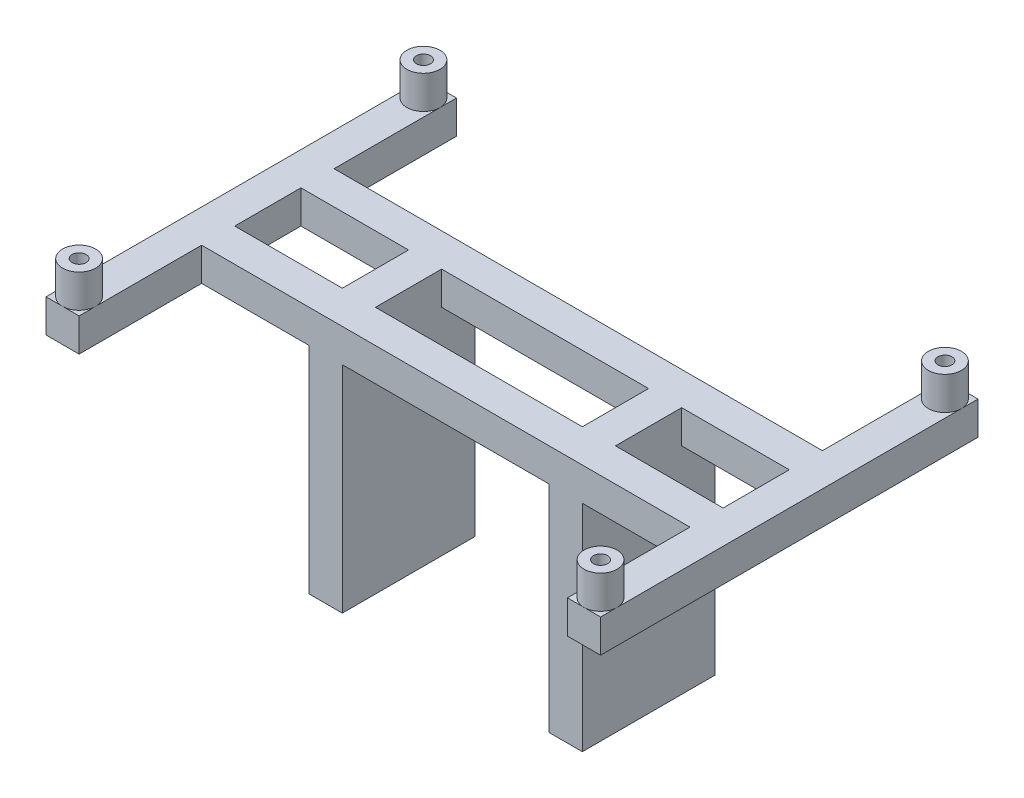
SolidWorks part; units mm, degrees
ref_plane "Front Plane" through (0, 0, 0) normal (0, 0, 1) x (1, 0, 0)
ref_plane "Top Plane" through (0, 0, 0) normal (0, 1, 0) x (1, 0, 0)
ref_plane "Right Plane" through (0, 0, 0) normal (1, 0, 0) x (0, 0, -1)
sketch "Sketch1" plane through (0, 0, 0) normal (0, 1, 0) x (1, 0, 0)
  line L28 (20.955, -5.08) -> (37.465, -5.08)
  line L31 (-42.545, 28.956) -> (-37.465, 28.956)
  line L32 (-42.545, 28.956) -> (-42.545, -28.956)
  line L33 (-42.545, -28.956) -> (-37.465, -28.956)
  line L34 (-37.465, 28.956) -> (-37.465, 10.16)
  line L35 (37.465, 28.956) -> (42.545, 28.956)
  line L36 (37.465, 28.956) -> (37.465, 10.16)
  line L37 (37.465, -28.956) -> (42.545, -28.956)
  line L38 (42.545, 28.956) -> (42.545, -28.956)
  line L39 (-37.465, 10.16) -> (37.465, 10.16)
  line L41 (-37.465, 5.08) -> (-20.955, 5.08)
  line L43 (-37.465, -5.08) -> (-20.955, -5.08)
  line L45 (-37.465, -10.16) -> (37.465, -10.16)
  line L48 (-20.955, 5.08) -> (-20.955, -5.08)
  line L50 (-15.875, 5.08) -> (-15.875, -5.08)
  line L52 (15.875, 5.08) -> (15.875, -5.08)
  line L54 (20.955, 5.08) -> (20.955, -5.08)
  line L55 (20.955, 5.08) -> (37.465, 5.08)
  line L56 (37.465, 5.08) -> (37.465, -5.08)
  line L57 (37.465, -10.16) -> (37.465, -28.956)
  line L58 (-15.875, -5.08) -> (15.875, -5.08)
  line L59 (-15.875, 5.08) -> (15.875, 5.08)
  line L60 (-37.465, 5.08) -> (-37.465, -5.08)
  line L61 (-37.465, -10.16) -> (-37.465, -28.956)
  point P25 (15.875, 0)
  point P26 (37.465, 0)
  point P27 (42.545, 0)
  point P28 (-20.955, 0)
  point P29 (0, 5.08)
  dimension "D1" = 57.912
  dimension "D2" = 5.08
  dimension "D3" = 5.08
  dimension "D4" = 20.32
  dimension "D5" = 41.91
  dimension "D6" = 5.08
  dimension "D7" = 5.08
  dimension "D8" = 5.08
  dimension "D9" = 85.09
extrude "Boss-Extrude1" add sketch "Sketch1" along normal blind 5.08
sketch "Sketch2" plane through (0, 0, 0) normal (0, -1, 0) x (1, 0, 0)
  line L1 (-20.955, 10.16) -> (-15.875, 10.16)
  line L2 (-20.955, 10.16) -> (-20.955, -10.16)
  line L3 (-20.955, -10.16) -> (-15.875, -10.16)
  line L4 (-15.875, 10.16) -> (-15.875, -10.16)
  line L6 (15.875, 10.16) -> (20.955, 10.16)
  line L7 (15.875, 10.16) -> (15.875, -10.16)
  line L8 (15.875, -10.16) -> (20.955, -10.16)
  line L9 (20.955, 10.16) -> (20.955, -10.16)
  line L12 (-20.955, 5.08) -> (-20.955, -5.08) construction
  line L13 (-15.875, -5.08) -> (-15.875, 5.08) construction
  line L14 (37.465, -10.16) -> (-37.465, -10.16) construction
  line L15 (-37.465, 10.16) -> (37.465, 10.16) construction
  line L16 (15.875, 5.08) -> (15.875, -5.08) construction
  line L17 (20.955, -5.08) -> (20.955, 5.08) construction
extrude "Boss-Extrude2" add sketch "Sketch2" along normal blind 33.02
sketch "Sketch4" plane through (0, 5.08, 0) normal (0, 1, 0) x (1, 0, 0)
  line L0 (-40.005, 26.416) -> (-40.005, -26.416) construction
  line L1 (40.005, 26.416) -> (40.005, -26.416) construction
  line L2 (-40.005, 0) -> (40.005, 0) construction
  circle A0 centre (-40.005, 26.416) radius 2.54
  circle A1 centre (-40.005, 26.416) radius 1.0795
  circle A2 centre (-40.005, -26.416) radius 1.0795
  circle A3 centre (-40.005, -26.416) radius 2.54
  circle A4 centre (40.005, -26.416) radius 1.0795
  circle A5 centre (40.005, -26.416) radius 2.54
  circle A6 centre (40.005, 26.416) radius 2.54
  circle A7 centre (40.005, 26.416) radius 1.0795
  point P12 (0, 0)
  dimension "D3" = 2.159
  dimension "D4" = 5.08
  dimension "D1" = 80.01
  dimension "D2" = 52.832
extrude "Boss-Extrude3" add sketch "Sketch4" along normal blind 5.08
sketch "Sketch5" plane through (0, 5.08, 0) normal (0, 1, 0) x (1, 0, 0)
  circle A1 centre (-40.005, -26.416) radius 1.0795
  circle A2 centre (-40.005, 26.416) radius 1.0795
  circle A3 centre (40.005, 26.416) radius 1.0795
  circle A4 centre (40.005, -26.416) radius 1.0795
  circle A5 centre (40.005, -26.416) radius 1.0795 construction
extrude "Cut-Extrude1" cut sketch "Sketch5" against normal through all
sketch "Sketch6" plane through (0, -33.02, 0) normal (0, -1, 0) x (1, 0, 0)
  line L0 (15.875, -10.16) -> (20.955, -10.16) construction
  line L1 (-20.955, -10.16) -> (-15.875, -10.16) construction
  line L2 (-18.415, 7.62) -> (-18.415, -7.62) construction
  circle A0 centre (-18.415, 7.62) radius 1.0795
  circle A1 centre (-18.415, -7.62) radius 1.0795
  circle A2 centre (18.415, 7.62) radius 1.0795
  circle A3 centre (18.415, -7.62) radius 1.0795
  point P8 (-18.415, 0)
  point P11 (18.415, -10.16)
  point P15 (-18.415, -10.16)
  dimension "D1" = 2.159
  dimension "D2" = 15.24
extrude "Cut-Extrude2" cut sketch "Sketch6" against normal blind 8.89
